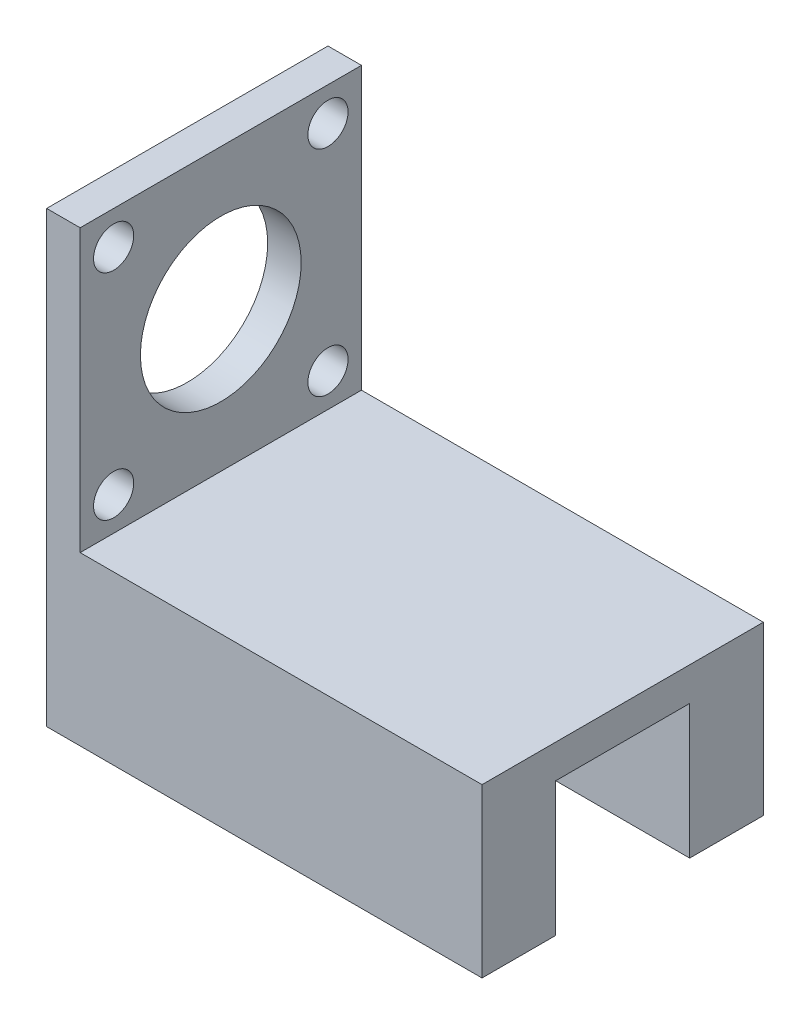
SolidWorks part; units mm, degrees
ref_plane "前视基准面" through (0, 0, 0) normal (0, 0, 1) x (1, 0, 0)
ref_plane "上视基准面" through (0, 0, 0) normal (0, 1, 0) x (1, 0, 0)
ref_plane "右视基准面" through (0, 0, 0) normal (1, 0, 0) x (0, 0, -1)
sketch "草图1" plane through (0, 0, 0) normal (0, 1, 0) x (1, 0, 0)
  line L0 (-24.486, -22.0265) -> (-24.486, -33.0265)
  line L1 (-24.486, 8.9735) -> (40.514, 8.9735)
  line L2 (-24.486, 8.9735) -> (-24.486, -2.0265)
  line L3 (-24.486, -33.0265) -> (40.514, -33.0265)
  line L4 (40.514, 8.9735) -> (40.514, -2.0265)
  line L5 (-24.486, 8.9735) -> (40.514, 8.9735)
  line L6 (-24.486, 8.9735) -> (-24.486, -2.0265)
  line L7 (-24.486, -2.0265) -> (40.514, -2.0265)
  line L8 (40.514, 8.9735) -> (40.514, -2.0265)
  line L9 (-24.486, -33.0265) -> (40.514, -33.0265)
  line L10 (-24.486, -33.0265) -> (-24.486, -22.0265)
  line L11 (-24.486, -22.0265) -> (40.514, -22.0265)
  line L12 (40.514, -33.0265) -> (40.514, -22.0265)
  line L13 (40.514, -22.0265) -> (40.514, -33.0265)
  dimension "D1" = 42
  dimension "D2" = 11
  dimension "D3" = 11
  dimension "D4" = 65
extrude "凸台-拉伸1" add sketch "草图1" along normal blind 20 contours L2 L7 L4 L1 | L3 L12 L11 L0
sketch "草图2" plane through (0, 20, 0) normal (0, 1, 0) x (1, 0, 0)
  line L0 (40.514, -33.0265) -> (40.514, -22.0265) construction
  line L1 (-24.486, 8.9735) -> (40.514, 8.9735)
  line L2 (-24.486, 8.9735) -> (-24.486, -33.0265)
  line L3 (-24.486, -33.0265) -> (40.514, -33.0265)
  line L4 (40.514, 8.9735) -> (40.514, -33.0265)
extrude "凸台-拉伸2" add sketch "草图2" along normal blind 5
sketch "草图3" plane through (0, 25, 0) normal (0, 1, 0) x (1, 0, 0)
  line L6 (40.514, 8.9735) -> (-24.486, 8.9735) construction
  line L7 (-24.486, -33.0265) -> (-19.486, -33.0265)
  line L8 (-24.486, -33.0265) -> (-24.486, 8.9735)
  line L9 (-24.486, 8.9735) -> (-19.486, 8.9735)
  line L10 (-19.486, -33.0265) -> (-19.486, 8.9735)
  dimension "D1" = 5
extrude "凸台-拉伸3" add sketch "草图3" along normal blind 42
sketch "草图5" plane through (-19.486, 0, 0) normal (1, 0, 0) x (0, 0, -1)
  line L0 (-33.0265, 67) -> (8.9735, 67) construction
  line L1 (-33.0265, 67) -> (-33.0265, 25) construction
  circle A0 centre (-12.0265, 46) radius 12
  circle A1 centre (-28.0265, 62) radius 3
  circle A8 centre (3.9735, 62) radius 3
  circle A9 centre (3.9735, 30) radius 3
  circle A10 centre (-28.0265, 30) radius 3
  point P17 (-7.0265, 56)
  point P18 (-9.5265, 48.5)
  point P19 (-12.0265, 46)
  dimension "D1" = 5
  dimension "D2" = 5
  dimension "D3" = 4
extrude "切除-拉伸3" cut sketch "草图5" against normal blind 42
